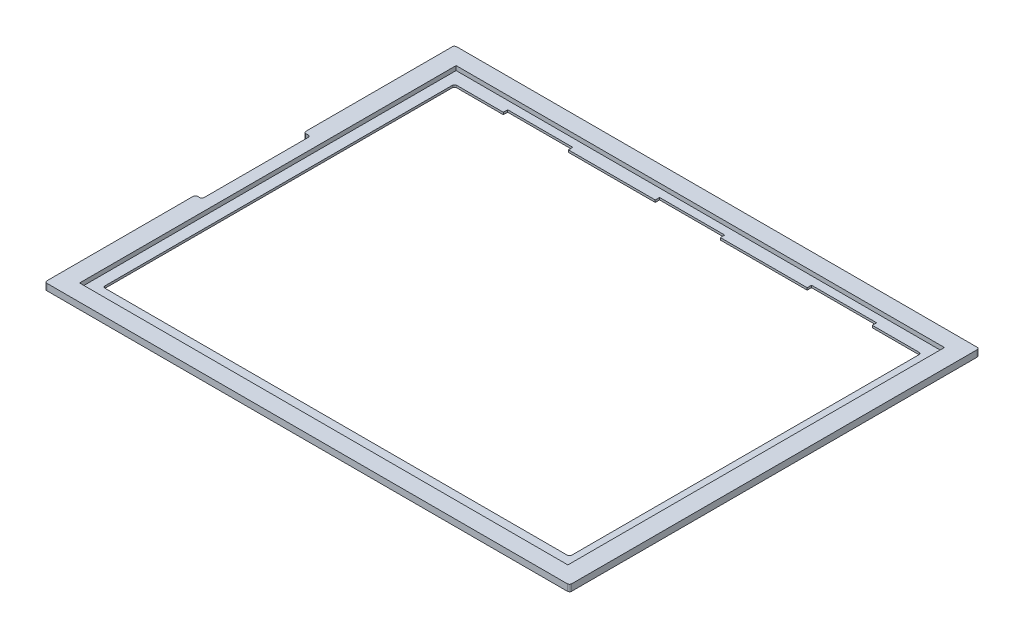
SolidWorks part; units mm, degrees
ref_plane "Front Plane" through (0, 0, 0) normal (0, 0, 1) x (1, 0, 0)
ref_plane "Top Plane" through (0, 0, 0) normal (0, 1, 0) x (1, 0, 0)
ref_plane "Right Plane" through (0, 0, 0) normal (1, 0, 0) x (0, 0, -1)
sketch "Sketch1" plane through (0, 0, 0) normal (0, 1, 0) x (1, 0, 0)
  line L0 (120.9, 188.8) -> (120.9, 220.5784) construction
  line L1 (0, 0) -> (241.8, 0)
  line L2 (0, 0) -> (0, 188.8)
  line L3 (0, 188.8) -> (241.8, 188.8)
  line L4 (241.8, 0) -> (241.8, 188.8)
  line L5 (13.4, 175.4) -> (228.4, 175.4)
  line L6 (13.4, 175.4) -> (13.4, 13.4)
  line L7 (13.4, 13.4) -> (228.4, 13.4)
  line L8 (228.4, 175.4) -> (228.4, 13.4)
  line L9 (0, 94.4) -> (-18.5526, 94.4) construction
  dimension "D1" = 188.8
  dimension "D2" = 241.8
  dimension "D3" = 215
  dimension "D4" = 162
extrude "Boss-Extrude1" add sketch "Sketch1" along normal blind 3
sketch "Sketch2" plane through (0, 3, 0) normal (0, 1, 0) x (1, 0, 0)
  line L0 (120.9, 188.8) -> (120.9, 201.4054) construction
  line L1 (8.4, 181.15) -> (233.4, 181.15)
  line L2 (8.4, 181.15) -> (8.4, 7.65)
  line L3 (8.4, 7.65) -> (233.4, 7.65)
  line L4 (233.4, 181.15) -> (233.4, 7.65)
  line L5 (241.8, 188.8) -> (0, 188.8) construction
  line L6 (0, 94.4) -> (-17.7147, 94.4) construction
  line L7 (0, 188.8) -> (0, 0) construction
  dimension "D1" = 173.5
  dimension "D2" = 225
extrude "Cut-Extrude1" cut sketch "Sketch2" against normal blind 2
sketch "Sketch3" plane through (0, 3, 0) normal (0, 1, 0) x (1, 0, 0)
  line L0 (0, 188.8) -> (0, 0) construction
  line L1 (0, 119.4) -> (3, 119.4)
  line L2 (0, 119.4) -> (0, 69.4)
  line L3 (0, 69.4) -> (3, 69.4)
  line L4 (3, 119.4) -> (3, 69.4)
  line L5 (13.4, 94.4) -> (28.3205, 94.4) construction
  line L6 (13.4, 175.4) -> (13.4, 13.4) construction
  dimension "D1" = 50
  dimension "D2" = 3
extrude "Cut-Extrude2" cut sketch "Sketch3" against normal blind 5
fillet "Fillet1" radius 1 12 edges at (228.4, 0.5, -13.4) (13.4, 0.5, -13.4) (13.4, 0.5, -175.4) (228.4, 0.5, -175.4) (0, 1.5, 0) (241.8, 1.5, 0) (241.8, 1.5, -188.8) (0, 1.5, -188.8) (3, 1.5, -69.4) (0, 1.5, -69.4) (0, 1.5, -119.4) (3, 1.5, -119.4)
sketch "Sketch4" plane through (0, 0, 0) normal (0, -1, 0) x (1, 0, 0)
  line L0 (227.4, -175.4) -> (14.4, -175.4) construction
  line L1 (35.9, -175.4) -> (65.9, -175.4)
  line L2 (35.9, -175.4) -> (35.9, -177.4)
  line L3 (35.9, -177.4) -> (65.9, -177.4)
  line L4 (65.9, -175.4) -> (65.9, -177.4)
  line L5 (120.9, -188.8) -> (120.9, -206.5842) construction
  line L6 (105.9, -175.4) -> (135.9, -175.4)
  line L7 (105.9, -175.4) -> (105.9, -177.4)
  line L8 (105.9, -177.4) -> (135.9, -177.4)
  line L9 (135.9, -175.4) -> (135.9, -177.4)
  line L10 (175.9, -175.4) -> (205.9, -175.4)
  line L11 (175.9, -175.4) -> (175.9, -177.4)
  line L12 (175.9, -177.4) -> (205.9, -177.4)
  line L13 (205.9, -175.4) -> (205.9, -177.4)
  line L14 (240.8, -188.8) -> (1, -188.8) construction
  dimension "D1" = 2
  dimension "D2" = 30
  dimension "D3" = 30
  dimension "D4" = 30
  dimension "D5" = 110
extrude "Cut-Extrude3" cut sketch "Sketch4" against normal through all
